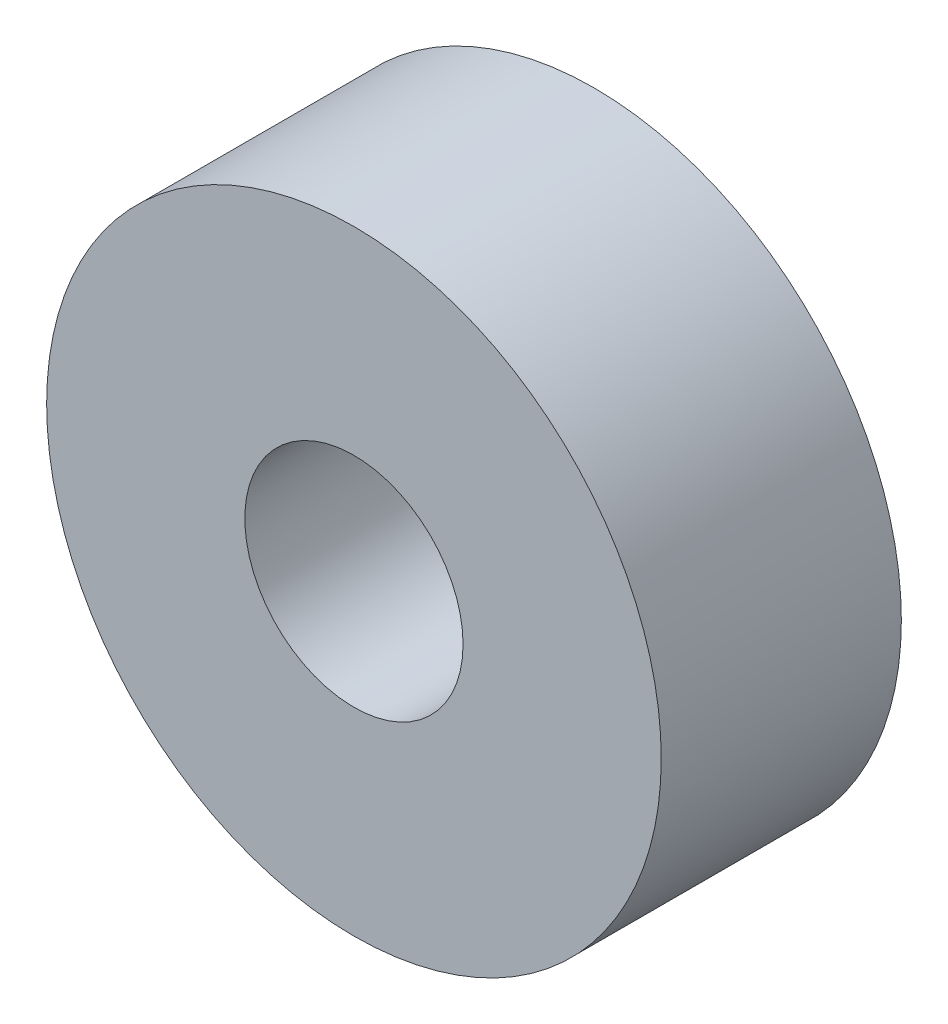
SolidWorks part; units mm, degrees
ref_plane "Front Plane" through (0, 0, 0) normal (0, 0, 1) x (1, 0, 0)
ref_plane "Top Plane" through (0, 0, 0) normal (0, 1, 0) x (1, 0, 0)
ref_plane "Right Plane" through (0, 0, 0) normal (1, 0, 0) x (0, 0, -1)
sketch "Sketch1" plane through (0, 0, 0) normal (0, 0, 1) x (1, 0, 0)
  circle A0 centre (0, 0) radius 11.176
  circle A1 centre (0, 0) radius 3.9688
  dimension "D1" = 22.352
  dimension "D2" = 7.9375
extrude "Boss-Extrude1" add sketch "Sketch1" along normal blind 8.7325
